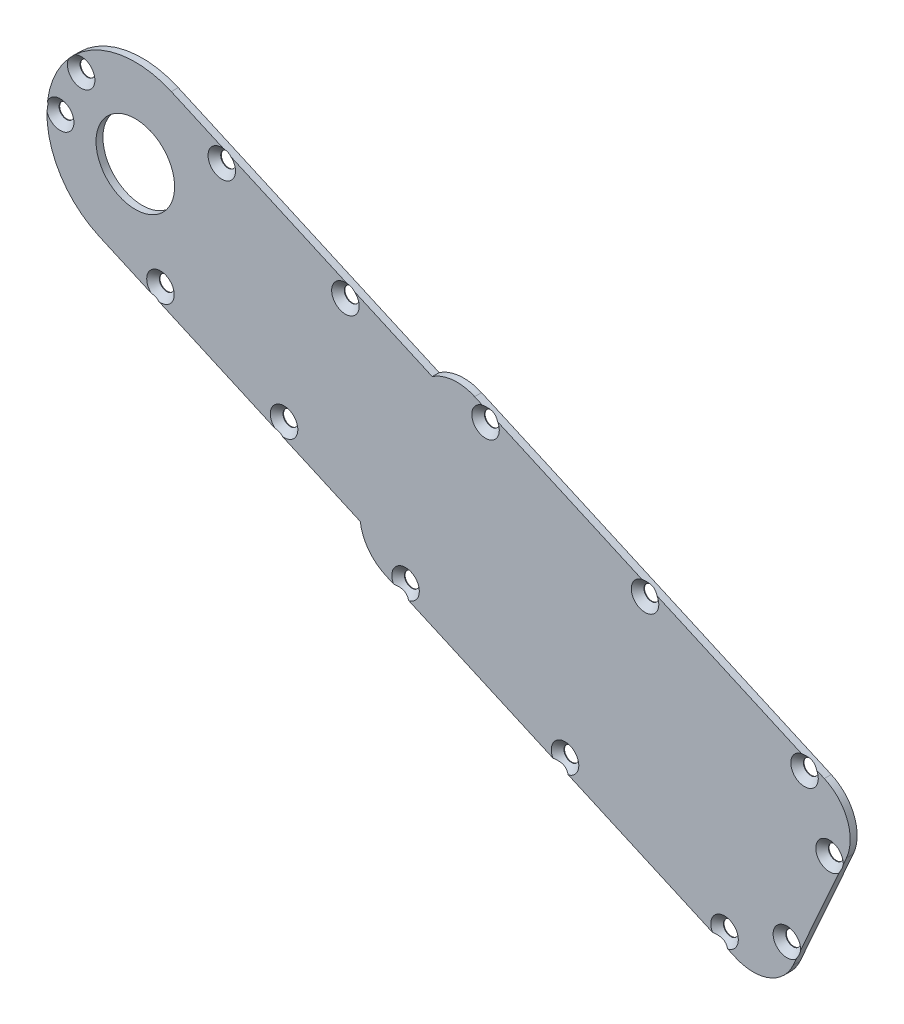
SolidWorks part; units mm, degrees
ref_plane "Front Plane" through (0, 0, 0) normal (0, 0, 1) x (1, 0, 0)
ref_plane "Top Plane" through (0, 0, 0) normal (0, 1, 0) x (1, 0, 0)
ref_plane "Right Plane" through (0, 0, 0) normal (1, 0, 0) x (0, 0, -1)
sketch "Sketch1" plane through (0, 0, 0) normal (0, 0, 1) x (1, 0, 0)
  line L0 (-21.9139, 59.5524) -> (-102.0156, 95.2596)
  line L1 (-111.7232, 94.3865) -> (-171.498, 121.0325)
  line L2 (-187.9877, 84.0414) -> (-128.2129, 57.3954)
  line L3 (-122.3733, 49.5916) -> (-42.2716, 13.8844)
  line L4 (-29.0664, 18.9465) -> (-16.8519, 46.3473)
  arc A0 (-16.8519, 46.3473) -> (-21.9139, 59.5524) centre (-25.9855, 50.4188) ccw
  arc A1 (-102.0156, 95.2596) -> (-111.7232, 94.3865) centre (-106.0872, 86.126) ccw
  arc A2 (-171.498, 121.0325) -> (-187.9877, 84.0414) centre (-179.7428, 102.5369) ccw
  arc A3 (-128.2129, 57.3954) -> (-122.3733, 49.5916) centre (-118.3017, 58.7252) ccw
  arc A4 (-42.2716, 13.8844) -> (-29.0664, 18.9465) centre (-38.2, 23.018) ccw
  circle A5 centre (-99.5171, 91.4087) radius 1.7
  circle A6 centre (-62.9827, 75.1226) radius 1.7
  circle A7 centre (-26.4483, 58.8365) radius 1.7
  circle A8 centre (-20.7221, 44.7879) radius 1.7
  circle A9 centre (-30.4937, 22.8673) radius 1.7
  circle A10 centre (-44.7701, 17.7353) radius 1.7
  circle A11 centre (-81.3045, 34.0214) radius 1.7
  circle A12 centre (-117.8389, 50.3075) radius 1.7
  circle A13 centre (-131.6182, 99.9706) radius 1.7
  circle A14 centre (-145.665, 68.4596) radius 1.7
  circle A15 centre (-173.9792, 81.0813) radius 1.7
  circle A16 centre (-159.9324, 112.5923) radius 1.7
  circle A17 centre (-192.146, 114.5254) radius 1.7
  circle A18 centre (-196.9503, 103.7481) radius 1.7
  dimension "D1" = 3.4
  dimension "D2" = 3.4
  dimension "D3" = 3.4
  dimension "D4" = 3.4
  dimension "D5" = 3.4
  dimension "D6" = 3.4
  dimension "D12" = 20.25
  dimension "D16" = 10
  dimension "D17" = 10
  dimension "D18" = 10
  dimension "D19" = 10
  dimension "D25" = 2.9
  dimension "D26" = 2.9
  dimension "D29" = 93.85
  dimension "D30" = 53.85
  dimension "D31" = 93.85
  dimension "D32" = 13.85
  dimension "D7" = 106.211
  dimension "D8" = 87.7
  dimension "D9" = 50
  dimension "D10" = 4.75
  dimension "D11" = 4.75
  dimension "D13" = 40.5
  dimension "D14" = 106.211
  dimension "D15" = 87.7
  dimension "D20" = 106.211
  dimension "D21" = 171.6559
  dimension "D22" = 30
  dimension "D23" = 10
  dimension "D24" = 10
  dimension "D27" = 13.85
  dimension "D28" = 53.85
extrude "Boss-Extrude1" add sketch "Sketch1" along normal blind 1.5875
sketch "Sketch2" plane through (0, 0, 0) normal (0, 0, -1) x (-1, 0, 0)
  circle A0 centre (179.7428, 102.5369) radius 9
  dimension "D1" = 18
extrude "Cut-Extrude1" cut sketch "Sketch2" against normal through all
hole_wizard "CSK for M3 Flat Head Machine Screw1" positions "Sketch4" profile "Sketch3" countersink size "M3" standard "ANSI Metric" end condition through all
sketch "Sketch4" plane through (0, 0, 1.5875) normal (0, 0, 1) x (1, 0, 0)
  point P0 (-192.146, 114.5254)
  point P3 (-196.9503, 103.7481)
  point P6 (-173.9792, 81.0813)
  point P9 (-145.665, 68.4596)
  point P12 (-117.8389, 50.3075)
  point P15 (-81.3045, 34.0214)
  point P18 (-44.7701, 17.7353)
  point P21 (-30.4937, 22.8673)
  point P24 (-20.7221, 44.7879)
  point P27 (-26.4483, 58.8365)
  point P30 (-62.9827, 75.1226)
  point P33 (-99.5171, 91.4087)
  point P36 (-131.6182, 99.9706)
  point P39 (-159.9324, 112.5923)
sketch "Sketch3" plane through (-192.146, 114.5254, 1.5875) normal (1, 0, 0) x (0, -1, 0)
  line L0 (0, 0) -> (0, 1.5875)
  line L1 (0, 1.5875) -> (1.7, 1.5875)
  line L2 (1.7, 1.5875) -> (1.7, 1.45)
  line L3 (1.7, 1.45) -> (3.15, 0)
  line L5 (3.15, 0) -> (0, 0)
  line L6 (-1.7, 1.45) -> (-3.15, 0) construction
  line L11 (0, -6.35) -> (0, 107.95) construction
  dimension "Thru Hole Dia." = 3.4
  dimension "Thru Hole Depth" = 1.5875
  dimension "Near C'Sink Dia." = 6.3
  dimension "Near C'Sink Angle" = 90
